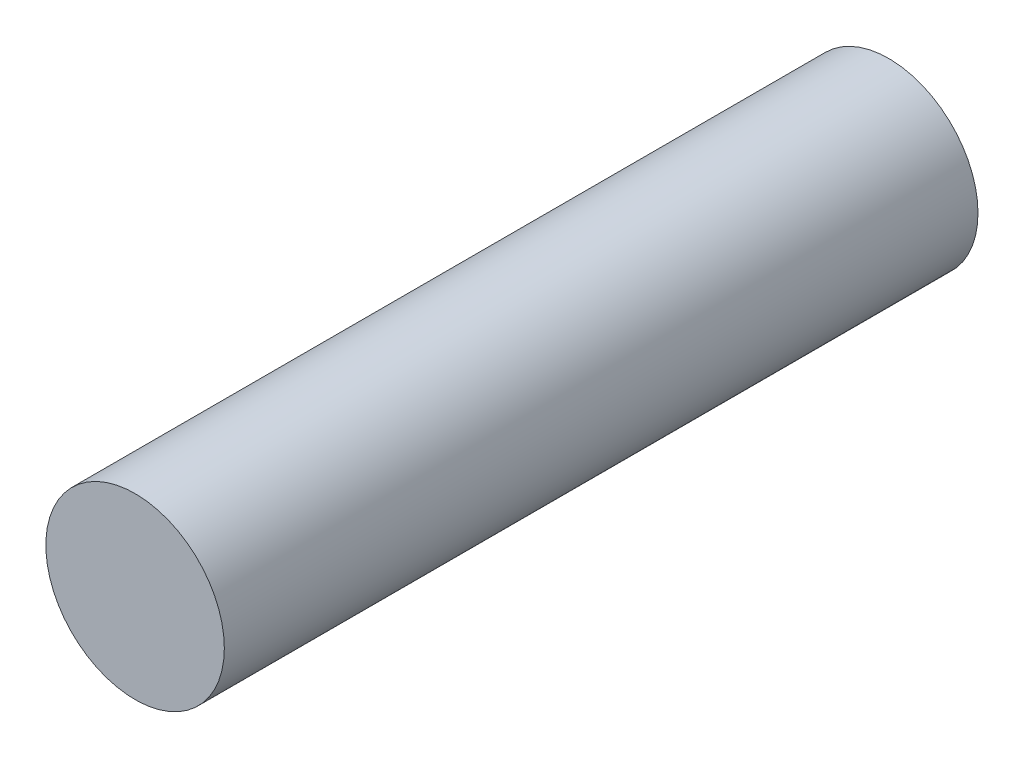
SolidWorks part; units mm, degrees
ref_plane "Front Plane" through (0, 0, 0) normal (0, 0, 1) x (1, 0, 0)
ref_plane "Top Plane" through (0, 0, 0) normal (0, 1, 0) x (1, 0, 0)
ref_plane "Right Plane" through (0, 0, 0) normal (1, 0, 0) x (0, 0, -1)
sketch "Sketch1" plane through (0, 0, 0) normal (0, 0, 1) x (1, 0, 0)
  circle A0 centre (0, 0) radius 9
  dimension "D1" = 18
extrude "Boss-Extrude1" add sketch "Sketch1" along normal blind 76
